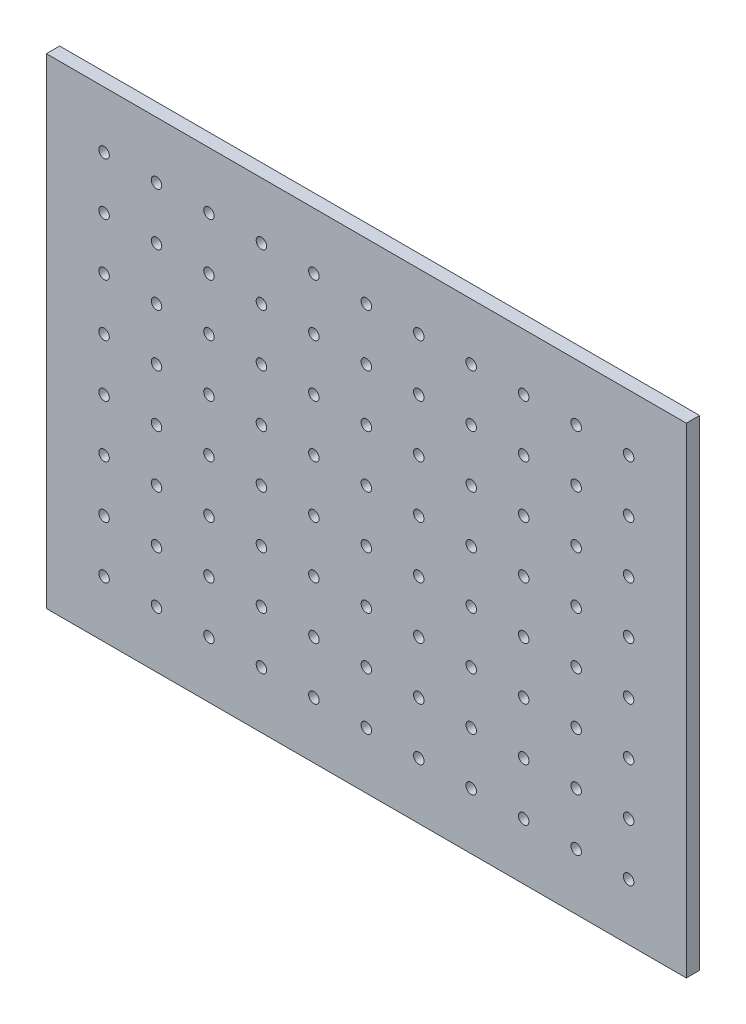
SolidWorks part; units mm, degrees
ref_plane "Plano frontal" through (0, 0, 0) normal (0, 0, 1) x (1, 0, 0)
ref_plane "Plano superior" through (0, 0, 0) normal (0, 1, 0) x (1, 0, 0)
ref_plane "Plano direito" through (0, 0, 0) normal (1, 0, 0) x (0, 0, -1)
sketch "Esboço2" plane through (0, 0, 0) normal (0, 0, 1) x (1, 0, 0)
  line L5 (-122.1306, 368.7676) -> (487.8694, 368.7676)
  line L6 (-122.1306, 368.7676) -> (-122.1306, -89.2324)
  line L7 (-122.1306, -89.2324) -> (487.8694, -89.2324)
  line L8 (487.8694, 368.7676) -> (487.8694, -89.2324)
  circle A88 centre (-67.1306, -35.2324) radius 5
  circle A89 centre (-17.1306, -35.2324) radius 5
  circle A90 centre (32.8694, -35.2324) radius 5
  circle A91 centre (82.8694, -35.2324) radius 5
  circle A92 centre (132.8694, -35.2324) radius 5
  circle A93 centre (182.8694, -35.2324) radius 5
  circle A94 centre (232.8694, -35.2324) radius 5
  circle A95 centre (282.8694, -35.2324) radius 5
  circle A96 centre (332.8694, -35.2324) radius 5
  circle A97 centre (382.8694, -35.2324) radius 5
  circle A98 centre (432.8694, -35.2324) radius 5
  circle A99 centre (-17.1306, 14.7676) radius 5
  circle A100 centre (32.8694, 14.7676) radius 5
  circle A101 centre (82.8694, 14.7676) radius 5
  circle A102 centre (132.8694, 14.7676) radius 5
  circle A103 centre (182.8694, 14.7676) radius 5
  circle A104 centre (232.8694, 14.7676) radius 5
  circle A105 centre (282.8694, 14.7676) radius 5
  circle A106 centre (332.8694, 14.7676) radius 5
  circle A107 centre (382.8694, 14.7676) radius 5
  circle A108 centre (432.8694, 14.7676) radius 5
  circle A109 centre (-17.1306, 64.7676) radius 5
  circle A110 centre (32.8694, 64.7676) radius 5
  circle A111 centre (82.8694, 64.7676) radius 5
  circle A112 centre (132.8694, 64.7676) radius 5
  circle A113 centre (182.8694, 64.7676) radius 5
  circle A114 centre (232.8694, 64.7676) radius 5
  circle A115 centre (282.8694, 64.7676) radius 5
  circle A116 centre (332.8694, 64.7676) radius 5
  circle A117 centre (382.8694, 64.7676) radius 5
  circle A118 centre (432.8694, 64.7676) radius 5
  circle A119 centre (-17.1306, 114.7676) radius 5
  circle A120 centre (32.8694, 114.7676) radius 5
  circle A121 centre (82.8694, 114.7676) radius 5
  circle A122 centre (132.8694, 114.7676) radius 5
  circle A123 centre (182.8694, 114.7676) radius 5
  circle A124 centre (232.8694, 114.7676) radius 5
  circle A125 centre (282.8694, 114.7676) radius 5
  circle A126 centre (332.8694, 114.7676) radius 5
  circle A127 centre (382.8694, 114.7676) radius 5
  circle A128 centre (432.8694, 114.7676) radius 5
  circle A129 centre (-17.1306, 164.7676) radius 5
  circle A130 centre (32.8694, 164.7676) radius 5
  circle A131 centre (82.8694, 164.7676) radius 5
  circle A132 centre (132.8694, 164.7676) radius 5
  circle A133 centre (182.8694, 164.7676) radius 5
  circle A134 centre (232.8694, 164.7676) radius 5
  circle A135 centre (282.8694, 164.7676) radius 5
  circle A136 centre (332.8694, 164.7676) radius 5
  circle A137 centre (382.8694, 164.7676) radius 5
  circle A138 centre (432.8694, 164.7676) radius 5
  circle A139 centre (-17.1306, 214.7676) radius 5
  circle A140 centre (32.8694, 214.7676) radius 5
  circle A141 centre (82.8694, 214.7676) radius 5
  circle A142 centre (132.8694, 214.7676) radius 5
  circle A143 centre (182.8694, 214.7676) radius 5
  circle A144 centre (232.8694, 214.7676) radius 5
  circle A145 centre (282.8694, 214.7676) radius 5
  circle A146 centre (332.8694, 214.7676) radius 5
  circle A147 centre (382.8694, 214.7676) radius 5
  circle A148 centre (432.8694, 214.7676) radius 5
  circle A149 centre (-17.1306, 264.7676) radius 5
  circle A150 centre (32.8694, 264.7676) radius 5
  circle A151 centre (82.8694, 264.7676) radius 5
  circle A152 centre (132.8694, 264.7676) radius 5
  circle A153 centre (182.8694, 264.7676) radius 5
  circle A154 centre (232.8694, 264.7676) radius 5
  circle A155 centre (282.8694, 264.7676) radius 5
  circle A156 centre (332.8694, 264.7676) radius 5
  circle A157 centre (382.8694, 264.7676) radius 5
  circle A158 centre (432.8694, 264.7676) radius 5
  circle A159 centre (-17.1306, 314.7676) radius 5
  circle A160 centre (32.8694, 314.7676) radius 5
  circle A161 centre (82.8694, 314.7676) radius 5
  circle A162 centre (132.8694, 314.7676) radius 5
  circle A163 centre (182.8694, 314.7676) radius 5
  circle A164 centre (232.8694, 314.7676) radius 5
  circle A165 centre (282.8694, 314.7676) radius 5
  circle A166 centre (332.8694, 314.7676) radius 5
  circle A167 centre (382.8694, 314.7676) radius 5
  circle A168 centre (432.8694, 314.7676) radius 5
  circle A169 centre (-67.1306, 14.7676) radius 5
  circle A170 centre (-67.1306, 64.7676) radius 5
  circle A171 centre (-67.1306, 114.7676) radius 5
  circle A172 centre (-67.1306, 164.7676) radius 5
  circle A173 centre (-67.1306, 214.7676) radius 5
  circle A174 centre (-67.1306, 264.7676) radius 5
  circle A175 centre (-67.1306, 314.7676) radius 5
  point P181 (-122.1306, 368.7676)
  point P182 (487.8694, -89.2324)
  dimension "D1" = 8
  dimension "D2" = 11
extrude "Ressalto-extrusão2" add sketch "Esboço2" along normal blind 12.7
